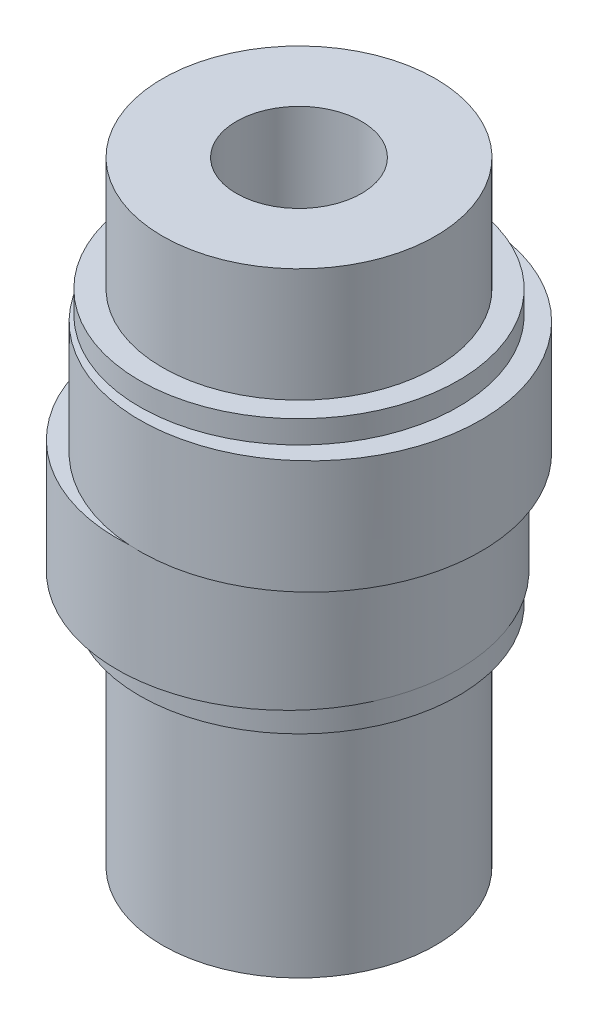
SolidWorks part; units mm, degrees
material "Custom Plastic-PLA"
ref_plane "Front Plane" through (0, 0, 0) normal (0, 0, 1) x (1, 0, 0)
ref_plane "Top Plane" through (0, 0, 0) normal (0, 1, 0) x (1, 0, 0)
ref_plane "Right Plane" through (0, 0, 0) normal (1, 0, 0) x (0, 0, -1)
sketch "Sketch1" plane through (0, 0, 0) normal (0, 1, 0) x (1, 0, 0)
  line L0 (0.5, 0) -> (-0.5, 0) construction
  circle A0 centre (-0.5, 0) radius 7.5
  point P4 (0, 0)
extrude "disk1" add sketch "Sketch1" along normal blind 5
sketch "Sketch2" plane through (0, 5, 0) normal (0, 1, 0) x (1, 0, 0)
  circle A0 centre (0.5, 0) radius 7.5
extrude "disk2" add sketch "Sketch2" along normal blind 5 contours A0
sketch "Sketch3" plane through (0, 10, 0) normal (0, 1, 0) x (1, 0, 0)
  circle A0 centre (0, 0) radius 7
extrude "tap-gap" add sketch "Sketch3" along normal blind 1
sketch "Sketch4" plane through (0, 11, 0) normal (0, 1, 0) x (1, 0, 0)
  circle A0 centre (0, 0) radius 6
extrude "top-bearing" add sketch "Sketch4" along normal blind 5
sketch "shaftmount" plane through (0, 0, 0) normal (0, 1, 0) x (1, 0, 0)
  circle A0 centre (0, 0) radius 7
extrude "gap" add sketch "shaftmount" against normal blind 1
sketch "Sketch8" plane through (0, -1, 0) normal (0, -1, 0) x (1, 0, 0)
  circle A0 centre (0, 0) radius 6
extrude "bearing" add sketch "Sketch8" along normal blind 5
sketch "Sketch9" plane through (0, -6, 0) normal (0, -1, 0) x (1, 0, 0)
  line L0 (-3, 4) -> (-3, -4)
  circle A0 centre (0, 0) radius 5
  circle A1 centre (0, 0) radius 6
  circle M2 centre (0, 0) radius 6
  dimension "D1" = 3
  dimension "D2" = 10
extrude "Boss-Extrude2" add sketch "Sketch9" along normal blind 5 contours L0 A0 | A0 M2
sketch "Sketch7" plane through (0, 0, 0) normal (0, 1, 0) x (1, 0, 0)
  circle A0 centre (0, 0) radius 2.75
  dimension "D1" = 5.5
extrude "holeCut" cut sketch "Sketch7" against normal through all and the other way through all
equation "\"3.5.00mm\"=3"
